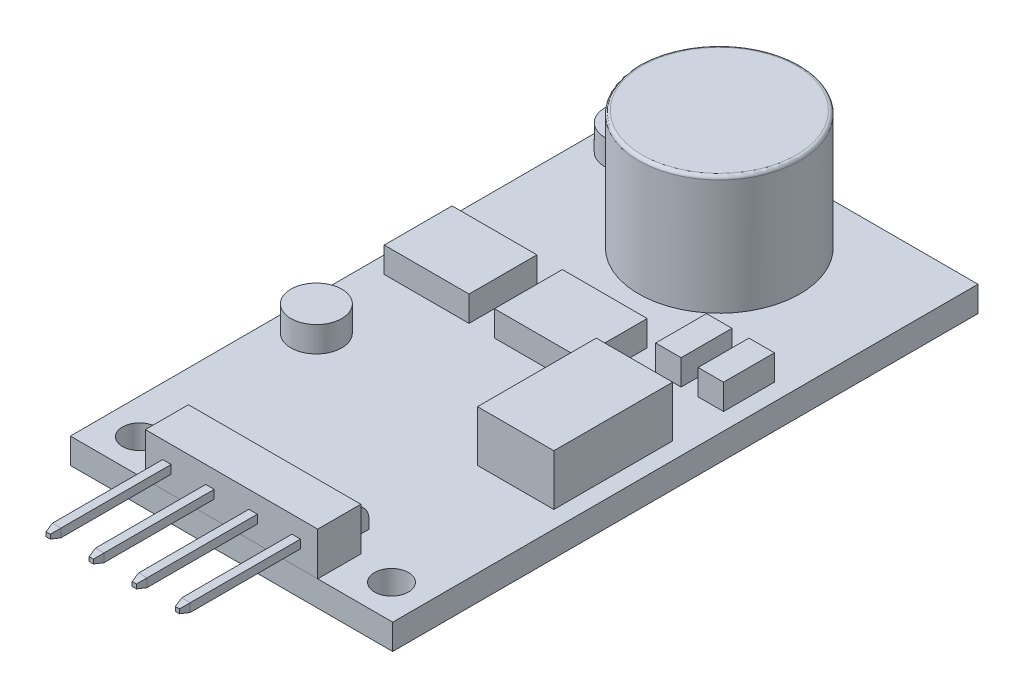
SolidWorks part; units mm, degrees
ref_plane "Front" through (0, 0, 0) normal (0, 0, 1) x (1, 0, 0)
ref_plane "Top" through (0, 0, 0) normal (0, 1, 0) x (1, 0, 0)
ref_plane "Right" through (0, 0, 0) normal (1, 0, 0) x (0, 0, -1)
sketch "Sketch1" plane through (0, 0, 0) normal (0, 1, 0) x (1, 0, 0)
  line L1 (-9.5, -17.25) -> (9.5, -17.25)
  line L2 (-9.5, -17.25) -> (-9.5, 17.25)
  line L3 (-9.5, 17.25) -> (9.5, 17.25)
  line L4 (9.5, -17.25) -> (9.5, 17.25)
  line L5 (-9.5, -17.25) -> (9.5, 17.25) construction
  line L6 (-9.5, 17.25) -> (9.5, -17.25) construction
  point P0 (0, 0)
  dimension "D1" = 19
  dimension "D2" = 34.5
extrude "Boss-Extrude1" add sketch "Sketch1" along normal blind 1.5
sketch "Sketch2" plane through (0, 1.5, 0) normal (0, 1, 0) x (1, 0, 0)
  line L0 (9.5, 17.25) -> (-9.5, 17.25) construction
  circle A0 centre (0, 11.5) radius 4.75
  point P2 (0, 11.4601)
  point P5 (0, 0)
  dimension "D1" = 9.5
  dimension "D2" = 1
extrude "Boss-Extrude2" add sketch "Sketch2" along normal blind 7
fillet "Fillet1" radius 0.2 1 edges at (0, 8.5, -6.75)
sketch "Sketch3" plane through (0, 1.5, 0) normal (0, 1, 0) x (1, 0, 0)
  line L0 (0, 0) -> (0, -17.25) construction
  line L1 (-9.5, -17.25) -> (9.5, -17.25) construction
  circle A0 centre (-7.43, -15.25) radius 1
  circle A1 centre (7.43, -15.25) radius 1
  dimension "D1" = 2
  dimension "D3" = 1
  dimension "D2" = 14.86
extrude "Cut-Extrude1" cut sketch "Sketch3" against normal through all
sketch "Sketch4" plane through (0, 1.5, 0) normal (0, 1, 0) x (1, 0, 0)
  line L0 (9.5, -17.25) -> (9.5, 17.25) construction
  line L1 (4, 0.25) -> (8.5, 0.25)
  line L2 (4, 0.25) -> (4, -6.75)
  line L3 (4, -6.75) -> (8.5, -6.75)
  line L4 (8.5, 0.25) -> (8.5, -6.75)
  line L5 (-9.5, -17.25) -> (9.5, -17.25) construction
  point P4 (3.3641, -4.6092)
  dimension "D1" = 4.5
  dimension "D2" = 7
  dimension "D3" = 1
  dimension "D4" = 10.5
extrude "Boss-Extrude3" add sketch "Sketch4" along normal blind 3
sketch "Sketch5" plane through (0, 1.5, 0) normal (0, 1, 0) x (1, 0, 0)
  line L0 (-9.5, 17.25) -> (-9.5, -17.25) construction
  line L1 (-8.5, 4.25) -> (-3.5, 4.25)
  line L2 (-8.5, 4.25) -> (-8.5, 0.25)
  line L3 (-8.5, 0.25) -> (-3.5, 0.25)
  line L4 (-3.5, 4.25) -> (-3.5, 0.25)
  line L5 (-2, 4.25) -> (3, 4.25)
  line L6 (-2, 4.25) -> (-2, 0.25)
  line L7 (-2, 0.25) -> (3, 0.25)
  line L8 (3, 4.25) -> (3, 0.25)
  line L9 (9.5, 17.25) -> (-9.5, 17.25) construction
  line L10 (9.5, -17.25) -> (9.5, 17.25) construction
  line L19 (4.5, 6.25) -> (6, 6.25)
  line L20 (4.5, 6.25) -> (4.5, 3.25)
  line L21 (4.5, 3.25) -> (6, 3.25)
  line L22 (6, 6.25) -> (6, 3.25)
  line L23 (7, 6.25) -> (8.5, 6.25)
  line L24 (7, 6.25) -> (7, 3.25)
  line L25 (7, 3.25) -> (8.5, 3.25)
  line L26 (8.5, 6.25) -> (8.5, 3.25)
  circle A0 centre (-7.5, 13.75) radius 1.5
  circle A1 centre (-7.5, -4.75) radius 1.5
  point P24 (8.8665, 5.0206)
  dimension "D6" = 3
  dimension "D8" = 18.5
  dimension "D9" = 2
  dimension "D1" = 5
  dimension "D2" = 4
  dimension "D3" = 1.5
  dimension "D4" = 1
  dimension "D5" = 13
  dimension "D7" = 3.5
  dimension "D10" = 3
  dimension "D11" = 1.5
  dimension "D12" = 1
  dimension "D13" = 1
  dimension "D14" = 11
extrude "Boss-Extrude4" add sketch "Sketch5" along normal blind 1.5
sketch "Sketch6" plane through (0, 1.5, 0) normal (0, 1, 0) x (1, 0, 0)
  line L1 (-5.08, -14.71) -> (5.08, -14.71)
  line L2 (-5.08, -14.71) -> (-5.08, -17.25)
  line L3 (-5.08, -17.25) -> (5.08, -17.25)
  line L4 (5.08, -14.71) -> (5.08, -17.25)
  line L5 (-9.5, -17.25) -> (9.5, -17.25) construction
  point P4 (0, -14.71)
  point P5 (-5.08, -16.449)
  point P7 (-5.08, -17.25)
  dimension "D1" = 10.16
  dimension "D2" = 2.54
extrude "Boss-Extrude5" add sketch "Sketch6" along normal blind 2.54 separate body
sketch "Sketch7" plane through (0, 0, 0) normal (1, 0, 0) x (0, 0, -1)
  line L0 (-13.21, 1.5) -> (-13.21, 2.02)
  line L1 (-17.25, 1.5) -> (17.25, 1.5) construction
  line L2 (-14.21, 3.02) -> (-24.25, 3.02)
  line L3 (-24.25, 3.02) -> (-24.25, 2.52)
  line L4 (-24.25, 2.52) -> (-14.21, 2.52)
  line L5 (-13.71, 2.02) -> (-13.71, 1.5)
  line L6 (-13.71, 1.5) -> (-13.21, 1.5)
  line L7 (-17.25, 2.77) -> (-24.25, 2.77) construction
  line L8 (-17.25, 4.04) -> (-17.25, 1.5) construction
  line L10 (-14.71, 4.04) -> (-14.71, 1.5) construction
  arc A0 (-13.21, 2.02) -> (-14.21, 3.02) centre (-14.21, 2.02) ccw
  arc A1 (-14.21, 2.52) -> (-13.71, 2.02) centre (-14.21, 2.02) cw
  point P16 (-14.1467, 2.52)
  point P17 (-13.8812, 1.5)
  point P20 (-13.71, 2.0194)
  dimension "D1" = 0.5
  dimension "D4" = 1
  dimension "D2" = 7
  dimension "D3" = 1.5
extrude "Boss-Extrude7" add sketch "Sketch7" along normal mid plane 0.5 from offset 1.27 separate body
chamfer "Chamfer1" distance 0.5 angle 14 4 edges at (1.27, 3.02, 24.25) (1.52, 2.77, 24.25) (1.27, 2.52, 24.25) (1.02, 2.77, 24.25)
pattern_linear "LPattern1" count 3 spacing 2.54 along (-1, 0, 0) count 2 spacing 2.54 along (1, 0, 0) of "Boss-Extrude7"
